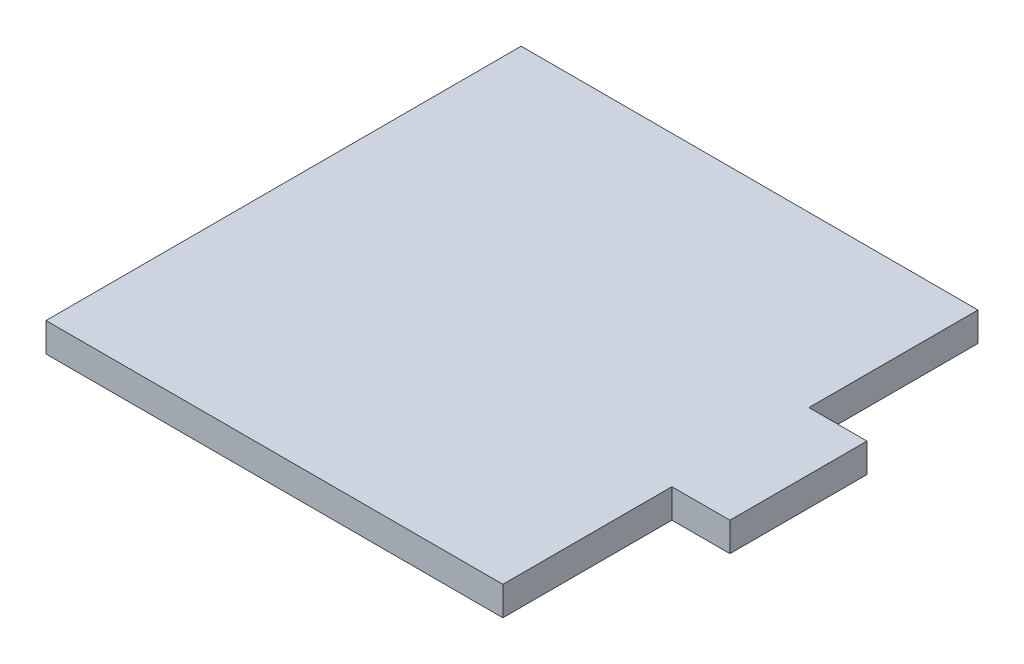
SolidWorks part; units mm, degrees
material "Cedar"
ref_plane "Front Plane" through (0, 0, 0) normal (0, 0, 1) x (1, 0, 0)
ref_plane "Top Plane" through (0, 0, 0) normal (0, 1, 0) x (1, 0, 0)
ref_plane "Right Plane" through (0, 0, 0) normal (1, 0, 0) x (0, 0, -1)
sketch "Sketch1" plane through (0, 0, 0) normal (0, 1, 0) x (1, 0, 0)
  line L0 (-25, 18.5) -> (25, 18.5)
  line L1 (25, 18.5) -> (25, 0)
  line L2 (25, 0) -> (31.35, 0)
  line L3 (31.35, 0) -> (31.35, -15)
  line L4 (31.35, -15) -> (25, -15)
  line L5 (25, -15) -> (25, -33.5)
  line L6 (25, -33.5) -> (-25, -33.5)
  line L7 (-25, -33.5) -> (-25, -15)
  line L8 (-25, -15) -> (-31.35, -15)
  line L9 (-31.35, -15) -> (-31.35, 0)
  line L10 (-31.35, 0) -> (-25, 0)
  line L11 (-25, 0) -> (-25, 18.5)
  line L12 (-25, 0) -> (-25, -15) construction
  point P11 (0, 18.5)
  point P14 (-31.35, -7.5)
  dimension "D1" = 6.35
  dimension "D2" = 15
  dimension "D3" = 50
  dimension "D4" = 52
extrude "Boss-Extrude1" add sketch "Sketch1" along normal blind 3.175 contours L11 L12 L7 L6 L5 L4 L3 L2 L1 L0
sketch "Sketch2" plane through (0, 3.175, 0) normal (0, 1, 0) x (1, 0, 0)
  line L8 (-25, 18.5) -> (-25, -33.5)
  line L9 (-25, -33.5) -> (25, -33.5)
  line L10 (25, -33.5) -> (25, -15)
  line L11 (25, -15) -> (31.35, -15)
  line L12 (31.35, -15) -> (31.35, 0)
  line L13 (31.35, 0) -> (25, 0)
  line L14 (25, 0) -> (25, 18.5)
  line L15 (25, 18.5) -> (-25, 18.5)
  line L16 (-25, 18.5) -> (-25, -33.5)
  line L17 (-25, -33.5) -> (25, -33.5)
  line L18 (25, -33.5) -> (25, -15)
  line L19 (25, -15) -> (31.35, -15)
  line L20 (31.35, -15) -> (31.35, 0)
  line L21 (31.35, 0) -> (25, 0)
  line L22 (25, 0) -> (25, 18.5)
  line L23 (25, 18.5) -> (-25, 18.5)
  dimension "D1" = 0
equation "\"length\"= 52mm"
equation "\"w_mach\"= 50mm"
equation "\"w_tab\"= 15mm"
equation "\"t_wood\"= 0.125in"
equation "\"t_side\"= 0.25in"
equation "\"D1@Sketch1\"=\"t_side\""
equation "\"D2@Sketch1\"=\"w_tab\""
equation "\"D3@Sketch1\"=\"w_mach\""
equation "\"D4@Sketch1\"=\"length\""
equation "\"D1@Boss-Extrude1\"=\"t_wood\""
